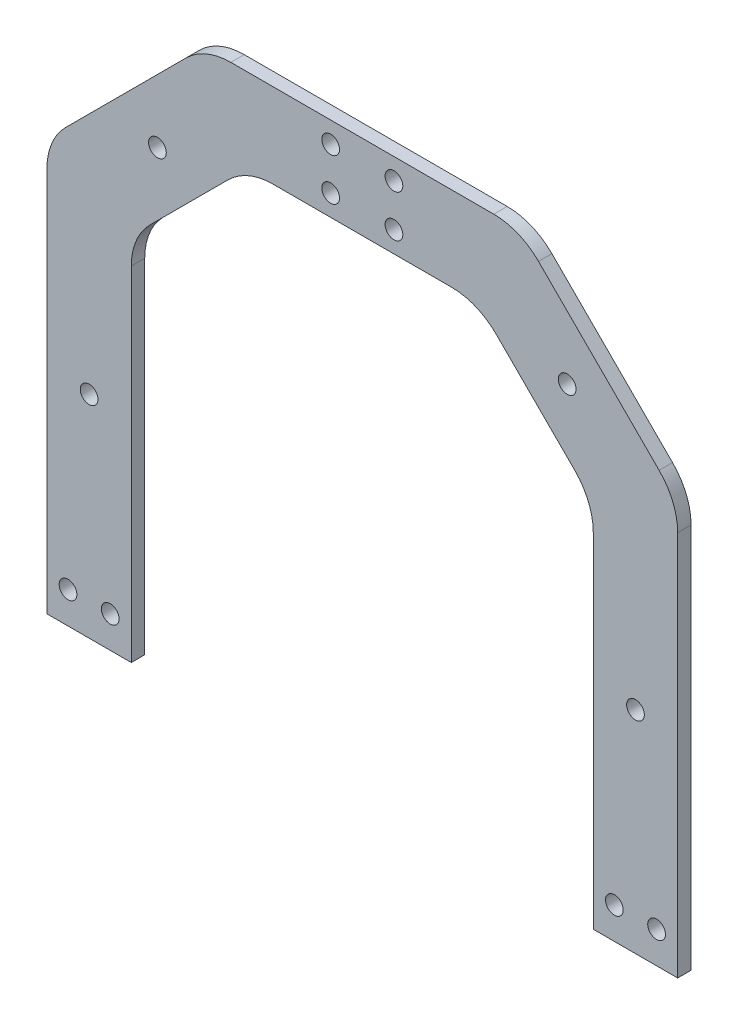
SolidWorks part; units mm, degrees
material "ASTM A36 Acero"
ref_plane "Alzado" through (0, 0, 0) normal (0, 0, 1) x (1, 0, 0)
ref_plane "Planta" through (0, 0, 0) normal (0, 1, 0) x (1, 0, 0)
ref_plane "Vista lateral" through (0, 0, 0) normal (1, 0, 0) x (0, 0, -1)
sketch "Croquis1" plane through (0, 0, 0) normal (0, 0, 1) x (1, 0, 0)
  line L0 (-119.5, 0) -> (119.5, 0) construction
  line L1 (-119.5, 0) -> (-139.5, 0) construction
  line L2 (0, -1000) -> (0, 49000) construction
  line L3 (119.5, 0) -> (139.5, 0) construction
  line L4 (-149.5, 0) -> (-109.5, 0) construction
  line L5 (149.5, 0) -> (109.5, 0) construction
  line L6 (0, 0) -> (0, 250) construction
  line L7 (0, 230) -> (0, 270) construction
  line L8 (-109.5, 0) -> (-109.5, 230) construction
  line L9 (-109.5, 230) -> (0, 230) construction
  line L10 (-63.5368, 221.2132) -> (-100.7132, 184.0368)
  line L11 (42.3236, 230) -> (-42.3236, 230)
  line L12 (-109.5, 162.8236) -> (-109.5, 0)
  line L13 (-149.5, 0) -> (-149.5, 270) construction
  line L14 (-149.5, 270) -> (0, 270) construction
  line L15 (-83.5368, 261.2132) -> (-140.7132, 204.0368)
  line L16 (62.3236, 270) -> (-62.3236, 270)
  line L17 (-149.5, 182.8236) -> (-149.5, 0)
  line L18 (149.5, 182.8236) -> (149.5, 0)
  line L19 (109.5, 162.8236) -> (109.5, 0)
  line L20 (83.5368, 261.2132) -> (140.7132, 204.0368)
  line L21 (63.5368, 221.2132) -> (100.7132, 184.0368)
  line L22 (-109.5, 0) -> (-149.5, 0)
  line L23 (109.5, 0) -> (149.5, 0)
  arc A0 (149.5, 182.8236) -> (140.7132, 204.0368) centre (119.5, 182.8236) ccw
  arc A1 (109.5, 162.8236) -> (100.7132, 184.0368) centre (79.5, 162.8236) ccw
  arc A2 (63.5368, 221.2132) -> (42.3236, 230) centre (42.3236, 200) ccw
  arc A3 (83.5368, 261.2132) -> (62.3236, 270) centre (62.3236, 240) ccw
  arc A4 (-83.5368, 261.2132) -> (-62.3236, 270) centre (-62.3236, 240) cw
  arc A5 (-140.7132, 204.0368) -> (-149.5, 182.8236) centre (-119.5, 182.8236) ccw
  arc A6 (-100.7132, 184.0368) -> (-109.5, 162.8236) centre (-79.5, 162.8236) ccw
  arc A7 (-63.5368, 221.2132) -> (-42.3236, 230) centre (-42.3236, 200) cw
  point P4 (0, 0)
  point P11 (-129.5, 0)
  point P17 (0, 250)
  point P30 (149.5, 195.25)
  point P33 (109.5, 175.25)
  point P36 (54.75, 230)
  point P39 (74.75, 270)
  point P42 (-74.75, 270)
  point P45 (-149.5, 195.25)
  point P48 (-109.5, 175.25)
  point P51 (-54.75, 230)
  dimension "D8" = 30
  dimension "D1" = 239
  dimension "D2" = 20
  dimension "D3" = 40
  dimension "D4" = 250
  dimension "D5" = 40
  dimension "D6" = 45
  dimension "D7" = 45
extrude "Saliente-Extruir1" add sketch "Croquis1" along normal blind 6.35
hole_wizard "Taladro de margen para M81" positions "Croquis2" profile "Croquis3" hole size "M8" standard "ISO" end condition through all
sketch "Croquis2" plane through (0, 0, 6.35) normal (0, 0, 1) x (1, 0, 0)
  line L0 (0, 0) -> (0, 15) construction
  line L2 (-119.5, 15) -> (-139.5, 15) construction
  line L4 (119.5, 15) -> (-119.5, 15) construction
  line L17 (0, 230) -> (0, 270) construction
  line L18 (-42.3236, 230) -> (42.3236, 230) construction
  line L19 (62.3236, 270) -> (-62.3236, 270) construction
  line L21 (-15, 240) -> (15, 240) construction
  line L22 (-15, 240) -> (-15, 260) construction
  line L23 (-15, 260) -> (15, 260) construction
  line L24 (15, 240) -> (15, 260) construction
  line L25 (-15, 240) -> (15, 260) construction
  line L26 (-15, 260) -> (15, 240) construction
  line L33 (-129.5, 185.25) -> (-129.5, 15) construction
  line L35 (0, 250) -> (-64.75, 250) construction
  line L38 (-64.75, 250) -> (-129.5, 185.25) construction
  line L40 (-100.7132, 184.0368) -> (-63.5368, 221.2132) construction
  line L41 (-83.5368, 261.2132) -> (-140.7132, 204.0368) construction
  point P0 (-119.5, 15)
  point P2 (-139.5, 15)
  point P35 (0, 15)
  point P137 (139.5, 15)
  point P144 (-15, 260)
  point P147 (-15, 240)
  point P150 (15, 240)
  point P153 (15, 260)
  point P169 (-129.5, 100.125)
  point P185 (-97.125, 217.625)
  point P190 (129.5, 100.125)
  point P191 (97.125, 217.625)
  point P194 (119.5, 15)
  dimension "D1" = 239
  dimension "D2" = 15
  dimension "D3" = 20
  dimension "D9" = 20
  dimension "D10" = 30
sketch "Croquis3" plane through (-119.5, 15, 6.35) normal (1, 0, 0) x (0, -1, 0)
  line L0 (0, 0) -> (0, 6.35)
  line L1 (0, 6.35) -> (4.2, 6.35)
  line L2 (4.2, 6.35) -> (4.2, 0)
  line L5 (4.2, 0) -> (0, 0)
  line L11 (0, -6.35) -> (0, 107.95) construction
  dimension "Diámetro de taladro hasta el siguiente" = 8.4
  dimension "Profundidad de taladro hasta el siguiente" = 6.35
